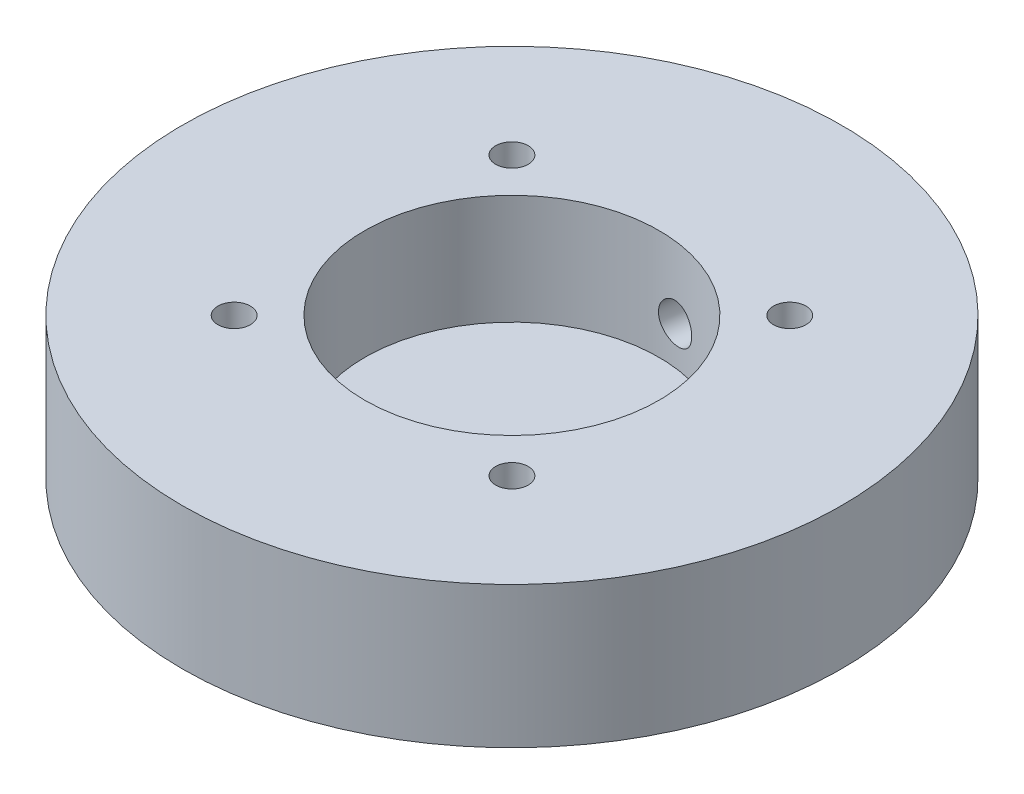
SolidWorks part; units mm, degrees
material "1060 Alloy"
ref_plane "Front Plane" through (0, 0, 0) normal (0, 0, 1) x (1, 0, 0)
ref_plane "Top Plane" through (0, 0, 0) normal (0, 1, 0) x (1, 0, 0)
ref_plane "Right Plane" through (0, 0, 0) normal (1, 0, 0) x (0, 0, -1)
sketch "Sketch2" plane through (0, 0, 0) normal (0, 1, 0) x (1, 0, 0)
  circle A0 centre (0, 0) radius 33.147
  dimension "D1" = 66.294
extrude "Boss-Extrude1" add sketch "Sketch2" along normal blind 14.224
sketch "Sketch3" [suppressed] plane through (0, 19.05, 0) normal (0, 1, 0) x (1, 0, 0)
  circle A0 centre (0, 0) radius 25.3111
  dimension "D1" = 50.6222
sketch "Sketch4" plane through (0, 14.224, 0) normal (0, 1, 0) x (1, 0, 0)
  circle A0 centre (0, 0) radius 14.7955
  dimension "D1" = 29.591
extrude "Cut-Extrude1" cut sketch "Sketch4" against normal offset from surface (11.049 mm away) 3.175 up to face at (0, 0, 33.147)
hole_wizard "#24 (0.152) Diameter Hole1" positions "3DSketch1" profile "Sketch5" hole size "#24" standard "ANSI Inch"
sketch3d "3DSketch1"
  point P0 (4.1997, 7.112, -32.8799)
  point P3 (55.0266, -11.2829, 0)
  dimension "D1" = 7.112
sketch "Sketch5" plane through (4.1997, 7.112, -32.8799) normal (0, 1, 0) x (-0.9919, 0, -0.1267)
  line L0 (0, 0) -> (0, 26.5599)
  line L1 (0, 26.5599) -> (1.9304, 25.4)
  line L2 (1.9304, 25.4) -> (1.9304, 0)
  line L5 (1.9304, 0) -> (0, 0)
  line L10 (0, 26.5599) -> (-1.9304, 25.4) construction
  line L11 (0, -6.35) -> (0, 107.95) construction
  dimension "Hole Dia." = 3.8608
  dimension "Hole Depth" = 25.4
  dimension "Drill Angle" = 118
hole_wizard "CBORE for #4 Binding Head Machine Screw1" positions "Sketch7" profile "Sketch8" counterbore size "#4" standard "ANSI Inch" end condition through all
sketch "Sketch7" plane through (0, 0, 0) normal (0, -1, 0) x (-1, 0, 0)
  line L0 (13.97, -13.97) -> (-13.97, -13.97) construction
  line L1 (-13.97, -13.97) -> (-13.97, 13.97) construction
  line L2 (13.97, 13.97) -> (13.97, -13.97) construction
  line L3 (-13.97, 13.97) -> (13.97, 13.97) construction
  line L4 (13.97, -13.97) -> (-13.97, -13.97) construction
  line L5 (-13.97, -13.97) -> (-13.97, 13.97) construction
  line L6 (13.97, 13.97) -> (13.97, -13.97) construction
  line L7 (-13.97, 13.97) -> (13.97, 13.97) construction
  point P0 (13.97, -13.97)
  point P1 (-13.97, -13.97)
  point P3 (-13.97, 13.97)
  point P4 (13.97, 13.97)
sketch "Sketch8" plane through (-13.97, 0, 13.97) normal (1, 0, 0) x (0, 0, -1)
  line L0 (0, 0) -> (0, 14.224)
  line L1 (0, 14.224) -> (1.6319, 14.224)
  line L3 (1.6319, 14.224) -> (1.6319, 11.049)
  line L4 (1.6319, 11.049) -> (3.3731, 11.049)
  line L5 (3.3731, 11.049) -> (3.3731, 0)
  line L7 (3.3731, 0) -> (0, 0)
  line L11 (0, -6.35) -> (0, 107.95) construction
  dimension "Thru Hole Dia." = 3.2639
  dimension "Thru Hole Depth" = 14.224
  dimension "C'Bore Dia." = 6.7462
  dimension "C'Bore Depth" = 11.049
